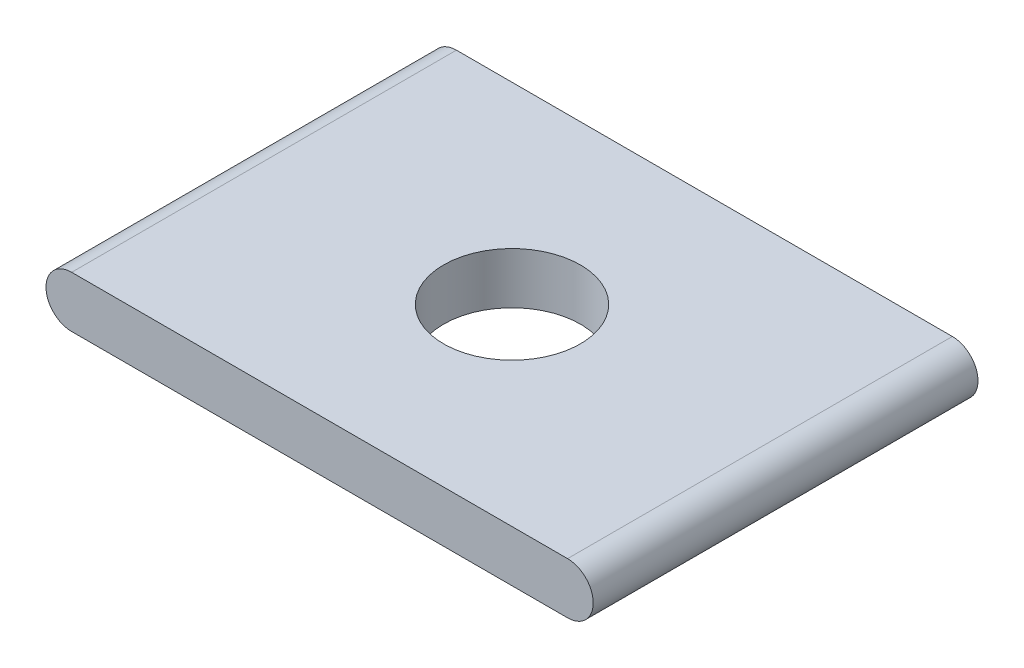
SolidWorks part; units mm, degrees
material "6061-T6 (SS)"
ref_plane "Front Plane" through (0, 0, 0) normal (0, 0, 1) x (1, 0, 0)
ref_plane "Top Plane" through (0, 0, 0) normal (0, 1, 0) x (1, 0, 0)
ref_plane "Right Plane" through (0, 0, 0) normal (1, 0, 0) x (0, 0, -1)
sketch "Sketch1" plane through (0, 0, 0) normal (0, 0, 1) x (1, 0, 0)
  line L0 (-18.415, 1.905) -> (18.415, 1.905)
  line L1 (18.415, -1.905) -> (-18.415, -1.905)
  arc A0 (18.415, 1.905) -> (18.415, -1.905) centre (18.415, 0) cw
  arc A1 (-18.415, -1.905) -> (-18.415, 1.905) centre (-18.415, 0) cw
  point P6 (0, 1.905)
  dimension "D1" = 1.905
  dimension "D2" = 36.83
extrude "Mount" add sketch "Sketch1" along normal blind 28.575
sketch "Sketch2" plane through (0, 1.905, 0) normal (0, 1, 0) x (1, 0, 0)
  line L0 (18.415, 0) -> (-18.415, 0) construction
  line L1 (18.415, -28.575) -> (18.415, 0) construction
  circle A0 centre (0, -14.2875) radius 5.08
  point P4 (0, 0)
  point P7 (18.415, -14.2875)
  dimension "D1" = 10.16
extrude "Hole" cut sketch "Sketch2" against normal through all
